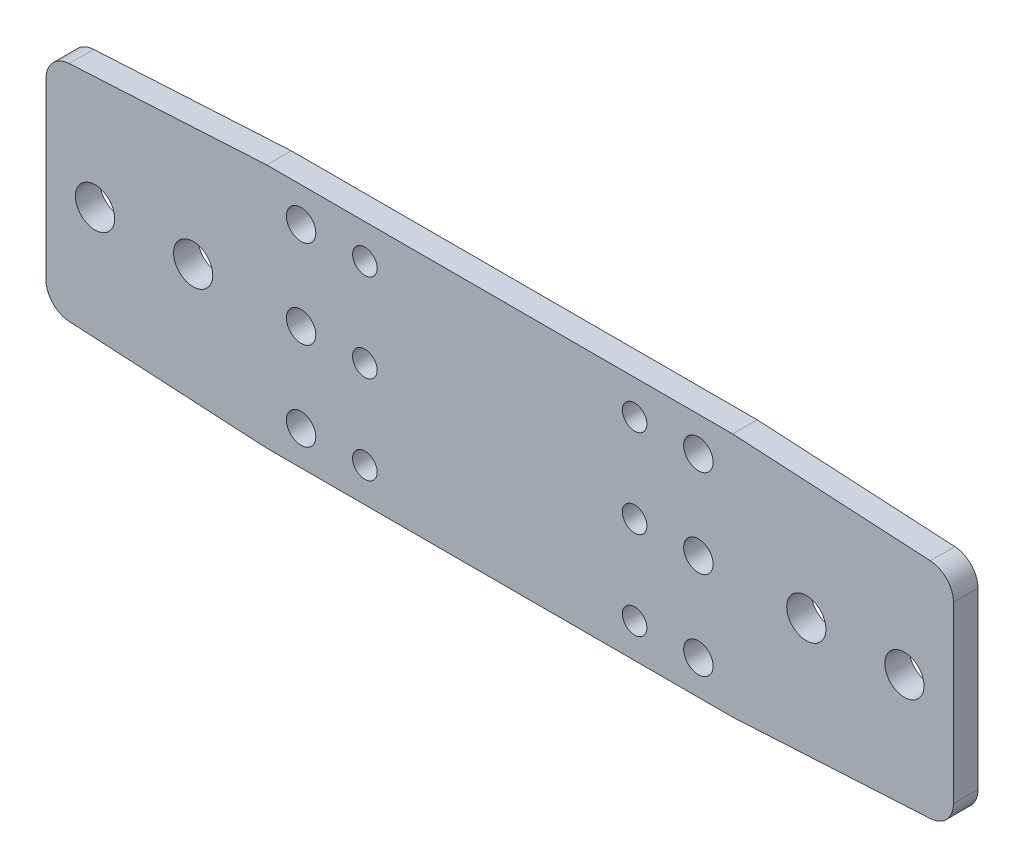
SolidWorks part; units mm, degrees
ref_plane "Płaszczyzna przednia" through (0, 0, 0) normal (0, 0, 1) x (1, 0, 0)
ref_plane "Płaszczyzna górna" through (0, 0, 0) normal (0, 1, 0) x (1, 0, 0)
ref_plane "Płaszczyzna prawa" through (0, 0, 0) normal (1, 0, 0) x (0, 0, -1)
sketch "Sketch1" plane through (0, 0, 0) normal (0, 0, 1) x (1, 0, 0)
  line L0 (0, -25) -> (95, -25) construction
  line L1 (47.5, 0) -> (47.5, -50) construction
  line L2 (7, -43) -> (25.8871, -43) construction
  line L3 (88, -7) -> (88, -43) construction
  line L4 (45.5, 0) -> (45.5, -50) construction
  line L5 (49.5, 0) -> (49.5, -50) construction
  line L6 (20, 0) -> (20, -50) construction
  line L7 (7, -7) -> (7, -25) construction
  line L8 (95, 0) -> (0, 0)
  line L9 (0, 0) -> (0, -50) construction
  line L10 (0, -50) -> (95, -50)
  line L11 (95, -50) -> (95, 0) construction
  line L12 (7, -25) -> (7, -43) construction
  line L13 (7, -7) -> (23.3918, -7) construction
  line L14 (0, -25) -> (-45, -25) construction
  line L15 (-45, -47.5) -> (-45, -2.5)
  line L16 (-45, -2.5) -> (0, 0)
  line L17 (-45, -47.5) -> (0, -50)
  line L18 (-22.5, -25) -> (-22.5, -21.253) construction
  line L19 (-35, -25) -> (-35, -21.253) construction
  line L20 (-15, -25) -> (-15, -21.253) construction
  line L21 (88, -7) -> (71.6082, -7) construction
  line L22 (75, 0) -> (75, -50) construction
  line L23 (88, -43) -> (69.1129, -43) construction
  line L24 (95, -25) -> (140, -25) construction
  line L25 (140, -47.5) -> (95, -50)
  line L26 (140, -2.5) -> (95, 0)
  line L27 (110, -25) -> (110, -21.253) construction
  line L28 (130, -25) -> (130, -21.253) construction
  line L29 (117.5, -25) -> (117.5, -21.253) construction
  line L30 (140, -47.5) -> (140, -2.5)
  circle A0 centre (-35, -25) radius 4
  circle A1 centre (-15, -25) radius 4
  circle A2 centre (75, -43) radius 2.5
  circle A3 centre (75, -7) radius 2.5
  circle A4 centre (110, -25) radius 4
  circle A5 centre (130, -25) radius 4
  circle A6 centre (20, -25) radius 2.5
  circle A7 centre (75, -25) radius 2.5
  arc A12 (7, -40) -> (7, -46) centre (7, -43) ccw
  arc A13 (7, -46) -> (7, -40) centre (7, -43) ccw
  arc A16 (88, -46) -> (88, -40) centre (88, -43) ccw
  arc A17 (88, -40) -> (88, -46) centre (88, -43) ccw
  arc A18 (88, -10) -> (88, -4) centre (88, -7) ccw
  arc A19 (88, -4) -> (88, -10) centre (88, -7) ccw
  arc A22 (7, -10) -> (7, -4) centre (7, -7) ccw
  arc A23 (7, -4) -> (7, -10) centre (7, -7) ccw
  circle A24 centre (7, -25) radius 3
  circle A25 centre (88, -25) radius 3
  circle A28 centre (20, -7) radius 2.5
  circle A29 centre (20, -43) radius 2.5
  point P40 (-45, -25)
  point P67 (140, -25)
  dimension "D3" = 3
  dimension "D6" = 6
  dimension "D7" = 6
  dimension "D11" = 5
  dimension "D12" = 5
  dimension "D17" = 8
  dimension "D18" = 8
  dimension "D19" = 5
  dimension "D20" = 5
  dimension "D1" = 95
  dimension "D2" = 50
  dimension "D4" = 7
  dimension "D5" = 7
  dimension "D10" = 20
  dimension "D13" = 45
  dimension "D14" = 45
  dimension "D8" = 2
  dimension "D9" = 2
  dimension "D15" = 12.5
  dimension "D16" = 7.5
extrude "Boss-Extrude1" add sketch "Sketch1" along normal blind 5
fillet "Fillet1" radius 5 4 edges at (140, -2.5, 2.5) (140, -47.5, 2.5) (-45, -2.5, 2.5) (-45, -47.5, 2.5)
